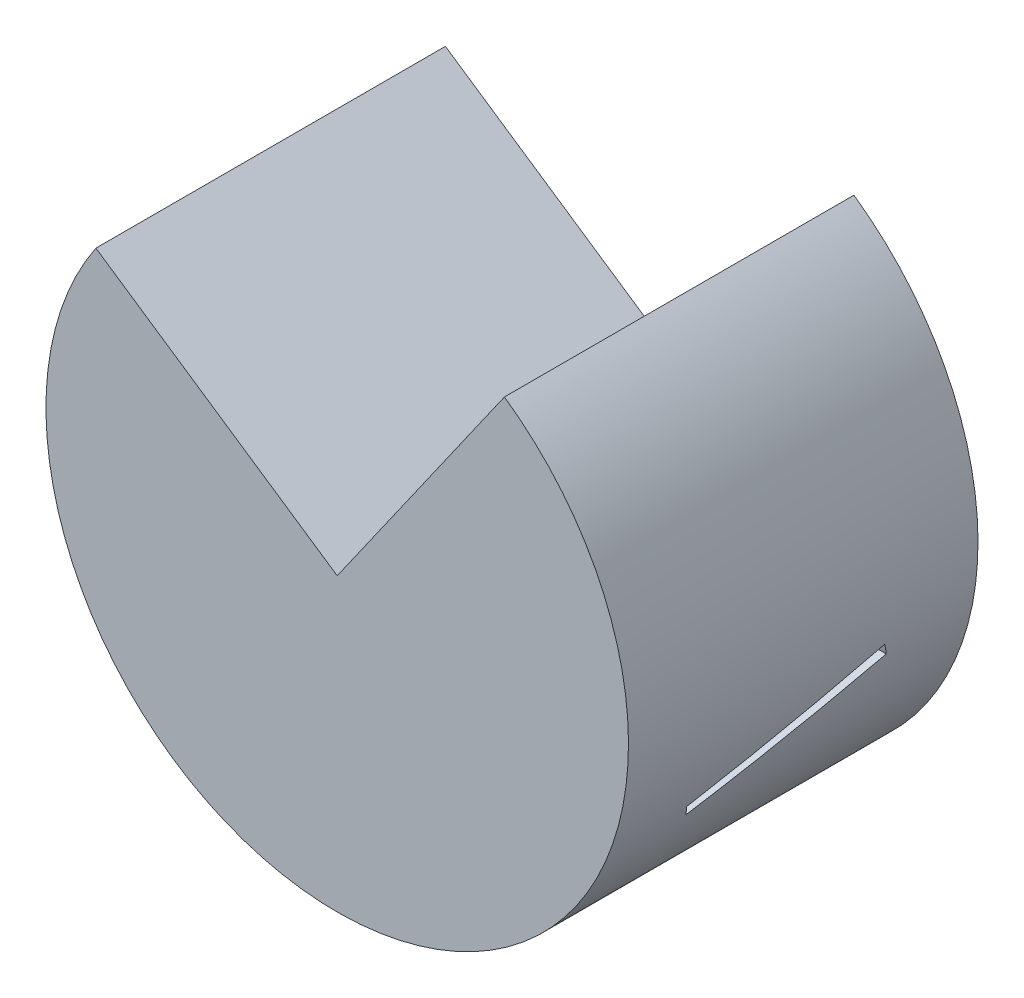
SolidWorks part; units mm, degrees
ref_plane "Front Plane" through (0, 0, 0) normal (0, 0, 1) x (1, 0, 0)
ref_plane "Top Plane" through (0, 0, 0) normal (0, 1, 0) x (1, 0, 0)
ref_plane "Right Plane" through (0, 0, 0) normal (1, 0, 0) x (0, 0, -1)
sketch "Sketch1" plane through (0, 0, 0) normal (0, 0, 1) x (1, 0, 0)
  circle A0 centre (0, 0) radius 25
  dimension "D1" = 50
extrude "Boss-Extrude1" add sketch "Sketch1" against normal mid plane 30
sketch "Sketch2" plane through (0, 0, 15) normal (0, 0, 1) x (1, 0, 0)
  line L0 (0, 0) -> (14.3532, 20.4692)
  line L1 (0, 0) -> (-20.7141, 13.9973)
  circle A1 centre (0, 0) radius 25
  circle A2 centre (0, 0) radius 25
  circle M2 centre (0, 0) radius 25
  dimension "D1" = 0
extrude "Cut-Extrude1" cut sketch "Sketch2" against normal blind 30 contours L1 L0 M2
sketch "Sketch3" plane through (0, 0, 0) normal (0, 0, 1) x (1, 0, 0)
  line L0 (10.2737, -12.7287) -> (15.7018, -19.4539)
  line L1 (10.2737, -12.7287) -> (0, 0) construction
  arc A0 (-20.7141, 13.9973) -> (14.3532, 20.4692) centre (0, 0) ccw construction
extrude "Cut-Extrude-Thin2" [suppressed] cut sketch "Sketch3" against normal mid plane 20 thin
sketch "Sketch4" plane through (0, 0, 0) normal (1, 0, 0) x (0, 0, -1)
  line L0 (-8.2795, -9.2018) -> (7.454, -4.3698)
extrude "Cut-Extrude-Thin3" cut sketch "Sketch4" against normal through all and the other way through all thin thin type mid plane wall 1
